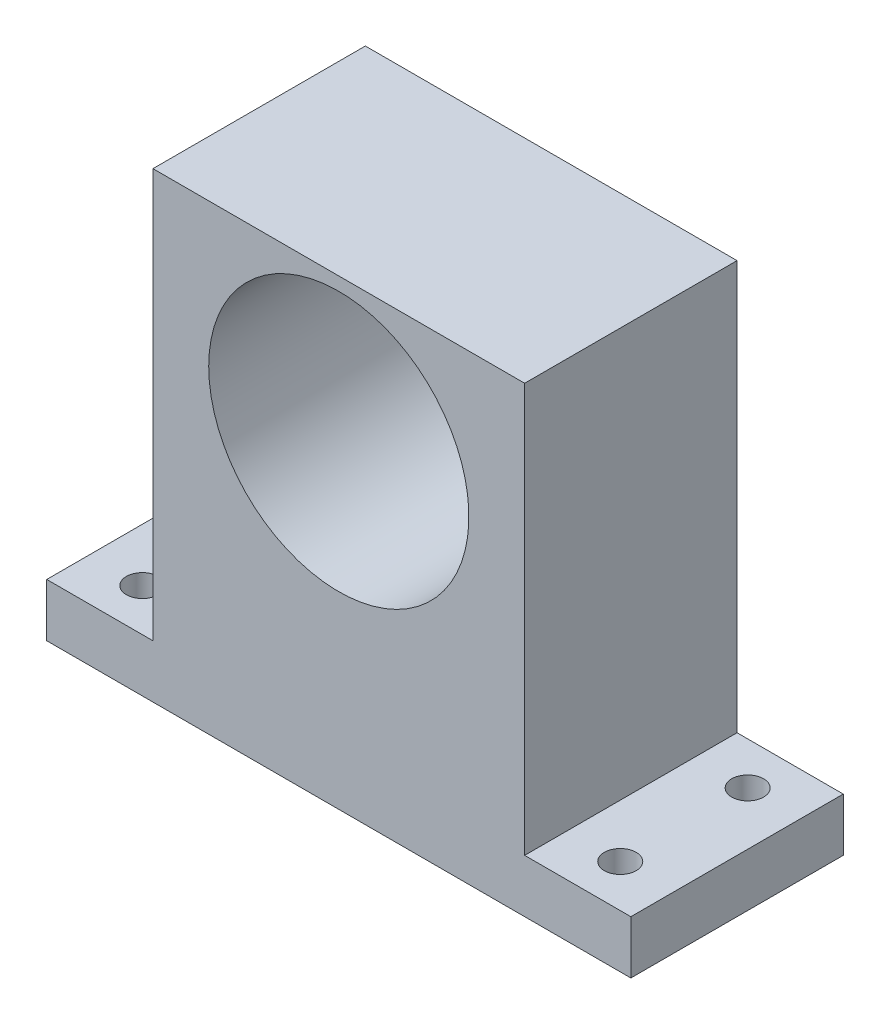
SolidWorks part; units mm, degrees
ref_plane "Спереди" through (0, 0, 0) normal (0, 0, 1) x (1, 0, 0)
ref_plane "Сверху" through (0, 0, 0) normal (0, 1, 0) x (1, 0, 0)
ref_plane "Справа" through (0, 0, 0) normal (1, 0, 0) x (0, 0, -1)
sketch "Эскиз1" plane through (0, 0, 0) normal (0, 0, 1) x (1, 0, 0)
  line L1 (-17.5, -21.75) -> (17.5, -21.75)
  line L2 (-17.5, -21.75) -> (-17.5, 21.75)
  line L3 (-17.5, 21.75) -> (17.5, 21.75)
  line L4 (17.5, -21.75) -> (17.5, 21.75)
  line L5 (-17.5, -21.75) -> (17.5, 21.75) construction
  line L6 (-17.5, 21.75) -> (17.5, -21.75) construction
  point P0 (0, 0)
  dimension "D1" = 35
  dimension "D2" = 43.5
extrude "Бобышка-Вытянуть1" add sketch "Эскиз1" along normal blind 20
sketch "Эскиз2" plane through (17.5, 0, 0) normal (1, 0, 0) x (0, 0, -1)
  line L0 (0, -21.75) -> (0, 21.75) construction
  line L1 (-20, -21.75) -> (0, -21.75)
  line L2 (-20, -21.75) -> (-20, -16.75)
  line L3 (-20, -16.75) -> (0, -16.75)
  line L4 (0, -21.75) -> (0, -16.75)
  dimension "D1" = 5
extrude "Бобышка-Вытянуть2" add sketch "Эскиз2" along normal blind 10
sketch "Эскиз3" plane through (-17.5, 0, 0) normal (-1, 0, 0) x (0, 0, 1)
  line L0 (20, 21.75) -> (20, -21.75) construction
  line L1 (0, -21.75) -> (20, -21.75)
  line L2 (0, -21.75) -> (0, -16.75)
  line L3 (0, -16.75) -> (20, -16.75)
  line L4 (20, -21.75) -> (20, -16.75)
  dimension "D1" = 5
extrude "Бобышка-Вытянуть3" add sketch "Эскиз3" along normal blind 10
sketch "Эскиз4" plane through (0, -16.75, 0) normal (0, 1, 0) x (1, 0, 0)
  line L0 (27.5, 0) -> (27.5, -20) construction
  line L1 (27.5, -20) -> (17.5, -20) construction
  line L2 (27.5, 0) -> (17.5, 0) construction
  line L3 (-27.5, -20) -> (-17.5, -20) construction
  line L4 (-27.5, -20) -> (-27.5, 0) construction
  line L5 (-27.5, 0) -> (-17.5, 0) construction
  circle A0 centre (-22.5, -16) radius 1.5
  circle A1 centre (-22.5, -4) radius 1.5
  circle A2 centre (22.5, -16) radius 1.5
  circle A3 centre (22.5, -4) radius 1.5
  point P8 (0, 0)
  point P15 (28.3893, -10.2762)
  point P20 (0, 0)
  dimension "D1" = 3
  dimension "D2" = 3
  dimension "D3" = 3
  dimension "D4" = 3
  dimension "D5" = 5
  dimension "D6" = 4
  dimension "D7" = 5
  dimension "D8" = 4
  dimension "D9" = 4
  dimension "D10" = 5
  dimension "D11" = 5
  dimension "D12" = 4
extrude "Вырез-Вытянуть2" cut sketch "Эскиз4" against normal blind 5
sketch "Эскиз5" plane through (0, 0, 0) normal (0, 0, -1) x (-1, 0, 0)
  line L0 (-17.5, -16.75) -> (-17.5, 21.75) construction
  line L1 (27.5, -21.75) -> (-27.5, -21.75) construction
  circle A0 centre (0, 8.25) radius 12.25
  dimension "D3" = 24.5
  dimension "D1" = 17.5
  dimension "D2" = 30
extrude "Вырез-Вытянуть3" cut sketch "Эскиз5" against normal blind 20
